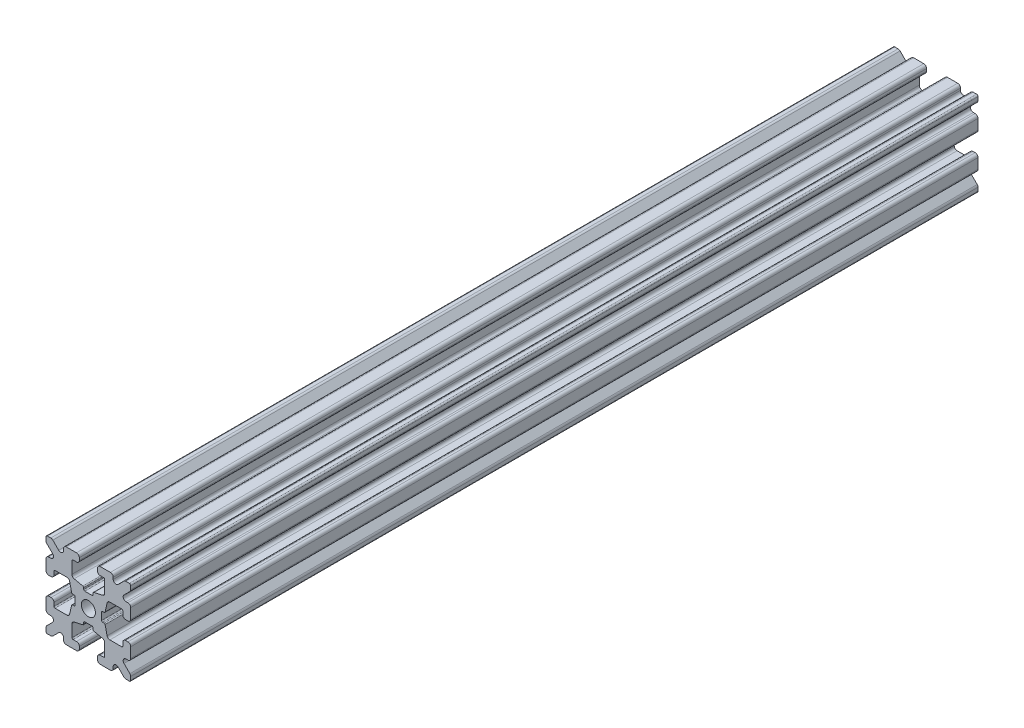
SolidWorks part; units mm, degrees
ref_plane "Front Plane" through (0, 0, 0) normal (0, 0, 1) x (1, 0, 0)
ref_plane "Top Plane" through (0, 0, 0) normal (0, 1, 0) x (1, 0, 0)
ref_plane "Right Plane" through (0, 0, 0) normal (1, 0, 0) x (0, 0, -1)
sketch "Profile" plane through (0, 0, 0) normal (0, 0, 1) x (1, 0, 0)
  line L0 (0.6255, -2.3471) -> (-0.6255, -2.3471)
  line L1 (-0.8255, -2.5471) -> (-0.8255, -2.7749)
  line L2 (-0.9818, -2.97) -> (-2.5094, -3.3124)
  line L3 (-2.9, -3.8003) -> (-2.9, -5.9)
  line L4 (-2.7, -6.1) -> (-2.1, -6.1)
  line L5 (-1.6, -6.6) -> (-1.6, -7)
  line L6 (-4.4, -7) -> (-4.4, -6.6678)
  line L7 (-5.2536, -6.3142) -> (-6.2929, -7.3536)
  line L8 (-7.3536, -6.2929) -> (-6.3142, -5.2536)
  line L9 (-6.6678, -4.4) -> (-7, -4.4)
  line L10 (-7.5, -2.1) -> (-7.5, -3.9)
  line L11 (-7, -1.6) -> (-6.6, -1.6)
  line L12 (-6.1, -2.1) -> (-6.1, -2.7)
  line L13 (-5.9, -2.9) -> (-3.8003, -2.9)
  line L14 (-3.3124, -2.5094) -> (-2.97, -0.9818)
  line L15 (-2.7749, -0.8255) -> (-2.5471, -0.8255)
  line L16 (-2.3471, -0.6255) -> (-2.3471, 0.6255)
  line L17 (-2.5471, 0.8255) -> (-2.7749, 0.8255)
  line L18 (-2.97, 0.9818) -> (-3.3124, 2.5094)
  line L19 (-3.8003, 2.9) -> (-5.9, 2.9)
  line L20 (-6.1, 2.7) -> (-6.1, 2.1)
  line L21 (-6.6, 1.6) -> (-7, 1.6)
  line L22 (-7, 4.4) -> (-6.6678, 4.4)
  line L23 (-6.3142, 5.2536) -> (-7.3536, 6.2929)
  line L24 (-6.2929, 7.3536) -> (-5.2536, 6.3142)
  line L25 (-4.4, 6.6678) -> (-4.4, 7)
  line L26 (-1.6, 7) -> (-1.6, 6.6)
  line L27 (-2.1, 6.1) -> (-2.7, 6.1)
  line L28 (-2.9, 5.9) -> (-2.9, 3.8003)
  line L29 (-2.5094, 3.3124) -> (-0.9818, 2.97)
  line L30 (-0.8255, 2.7749) -> (-0.8255, 2.5471)
  line L31 (-0.6255, 2.3471) -> (0.6255, 2.3471)
  line L32 (0.8255, 2.5471) -> (0.8255, 2.7749)
  line L33 (0.9818, 2.97) -> (2.5094, 3.3124)
  line L34 (2.9, 3.8003) -> (2.9, 5.9)
  line L35 (2.7, 6.1) -> (2.1, 6.1)
  line L36 (1.6, 6.6) -> (1.6, 7)
  line L37 (4.4, 7) -> (4.4, 6.6678)
  line L38 (5.2536, 6.3142) -> (6.2929, 7.3536)
  line L39 (7.25, 7.5) -> (6.6464, 7.5)
  line L40 (7.3536, 6.2929) -> (6.3142, 5.2536)
  line L41 (6.6678, 4.4) -> (7, 4.4)
  line L42 (7, 1.6) -> (6.6, 1.6)
  line L43 (6.1, 2.1) -> (6.1, 2.7)
  line L44 (5.9, 2.9) -> (3.8003, 2.9)
  line L45 (3.3124, 2.5094) -> (2.97, 0.9818)
  line L46 (2.7749, 0.8255) -> (2.5471, 0.8255)
  line L47 (2.3471, 0.6255) -> (2.3471, -0.6255)
  line L48 (2.5471, -0.8255) -> (2.7749, -0.8255)
  line L49 (2.97, -0.9818) -> (3.3124, -2.5094)
  line L50 (3.8003, -2.9) -> (5.9, -2.9)
  line L51 (6.1, -2.7) -> (6.1, -2.1)
  line L52 (6.6, -1.6) -> (7, -1.6)
  line L53 (7.5, -3.9) -> (7.5, -2.1)
  line L54 (7, -4.4) -> (6.6678, -4.4)
  line L55 (6.3142, -5.2536) -> (7.3536, -6.2929)
  line L56 (6.6464, -7.5) -> (7.25, -7.5)
  line L57 (6.2929, -7.3536) -> (5.2536, -6.3142)
  line L58 (4.4, -6.6678) -> (4.4, -7)
  line L59 (1.6, -7) -> (1.6, -6.6)
  line L60 (2.1, -6.1) -> (2.7, -6.1)
  line L61 (2.9, -5.9) -> (2.9, -3.8003)
  line L62 (2.5094, -3.3124) -> (0.9818, -2.97)
  line L63 (0.8255, -2.7749) -> (0.8255, -2.5471)
  line L64 (-7.5, 3.9) -> (-7.5, 2.1)
  line L65 (-6.6464, 7.5) -> (-7.25, 7.5)
  line L66 (-3.9, -7.5) -> (-2.1, -7.5)
  line L67 (7.5, 2.1) -> (7.5, 3.9)
  line L68 (-7.5, 7.25) -> (-7.5, 6.6464)
  line L69 (7.5, -7.25) -> (7.5, -6.6464)
  line L70 (7.5, 6.6464) -> (7.5, 7.25)
  line L71 (-2.1, 7.5) -> (-3.9, 7.5)
  line L72 (-7.5, -6.6464) -> (-7.5, -7.25)
  line L73 (3.9, 7.5) -> (2.1, 7.5)
  line L74 (2.1, -7.5) -> (3.9, -7.5)
  line L75 (-7.25, -7.5) -> (-6.6464, -7.5)
  circle A0 centre (0, 0) radius 1.25
  arc A1 (0.8255, -2.5471) -> (0.6255, -2.3471) centre (0.6255, -2.5471) ccw
  arc A2 (-0.6255, -2.3471) -> (-0.8255, -2.5471) centre (-0.6255, -2.5471) ccw
  arc A3 (-0.9818, -2.97) -> (-0.8255, -2.7749) centre (-1.0255, -2.7749) ccw
  arc A4 (-2.5094, -3.3124) -> (-2.9, -3.8003) centre (-2.4, -3.8003) ccw
  arc A5 (-2.9, -5.9) -> (-2.7, -6.1) centre (-2.7, -5.9) ccw
  arc A6 (-1.6, -6.6) -> (-2.1, -6.1) centre (-2.1, -6.6) ccw
  arc A7 (-2.1, -7.5) -> (-1.6, -7) centre (-2.1, -7) ccw
  arc A8 (-4.4, -7) -> (-3.9, -7.5) centre (-3.9, -7) ccw
  arc A9 (-4.4, -6.6678) -> (-5.2536, -6.3142) centre (-4.9, -6.6678) ccw
  arc A10 (-6.6464, -7.5) -> (-6.2929, -7.3536) centre (-6.6464, -7) ccw
  arc A11 (-7.5, -7.25) -> (-7.25, -7.5) centre (-7.25, -7.25) ccw
  arc A12 (-7.3536, -6.2929) -> (-7.5, -6.6464) centre (-7, -6.6464) ccw
  arc A13 (-6.3142, -5.2536) -> (-6.6678, -4.4) centre (-6.6678, -4.9) ccw
  arc A14 (-7.5, -3.9) -> (-7, -4.4) centre (-7, -3.9) ccw
  arc A15 (-7, -1.6) -> (-7.5, -2.1) centre (-7, -2.1) ccw
  arc A16 (-6.1, -2.1) -> (-6.6, -1.6) centre (-6.6, -2.1) ccw
  arc A17 (-6.1, -2.7) -> (-5.9, -2.9) centre (-5.9, -2.7) ccw
  arc A18 (-3.8003, -2.9) -> (-3.3124, -2.5094) centre (-3.8003, -2.4) ccw
  arc A19 (-2.7749, -0.8255) -> (-2.97, -0.9818) centre (-2.7749, -1.0255) ccw
  arc A20 (-2.5471, -0.8255) -> (-2.3471, -0.6255) centre (-2.5471, -0.6255) ccw
  arc A21 (-2.3471, 0.6255) -> (-2.5471, 0.8255) centre (-2.5471, 0.6255) ccw
  arc A22 (-2.97, 0.9818) -> (-2.7749, 0.8255) centre (-2.7749, 1.0255) ccw
  arc A23 (-3.3124, 2.5094) -> (-3.8003, 2.9) centre (-3.8003, 2.4) ccw
  arc A24 (-5.9, 2.9) -> (-6.1, 2.7) centre (-5.9, 2.7) ccw
  arc A25 (-6.6, 1.6) -> (-6.1, 2.1) centre (-6.6, 2.1) ccw
  arc A26 (-7.5, 2.1) -> (-7, 1.6) centre (-7, 2.1) ccw
  arc A27 (-7, 4.4) -> (-7.5, 3.9) centre (-7, 3.9) ccw
  arc A28 (-6.6678, 4.4) -> (-6.3142, 5.2536) centre (-6.6678, 4.9) ccw
  arc A29 (-7.5, 6.6464) -> (-7.3536, 6.2929) centre (-7, 6.6464) ccw
  arc A30 (-7.25, 7.5) -> (-7.5, 7.25) centre (-7.25, 7.25) ccw
  arc A31 (-6.2929, 7.3536) -> (-6.6464, 7.5) centre (-6.6464, 7) ccw
  arc A32 (-5.2536, 6.3142) -> (-4.4, 6.6678) centre (-4.9, 6.6678) ccw
  arc A33 (-3.9, 7.5) -> (-4.4, 7) centre (-3.9, 7) ccw
  arc A34 (-1.6, 7) -> (-2.1, 7.5) centre (-2.1, 7) ccw
  arc A35 (-2.1, 6.1) -> (-1.6, 6.6) centre (-2.1, 6.6) ccw
  arc A36 (-2.7, 6.1) -> (-2.9, 5.9) centre (-2.7, 5.9) ccw
  arc A37 (-2.9, 3.8003) -> (-2.5094, 3.3124) centre (-2.4, 3.8003) ccw
  arc A38 (-0.8255, 2.7749) -> (-0.9818, 2.97) centre (-1.0255, 2.7749) ccw
  arc A39 (-0.8255, 2.5471) -> (-0.6255, 2.3471) centre (-0.6255, 2.5471) ccw
  arc A40 (0.6255, 2.3471) -> (0.8255, 2.5471) centre (0.6255, 2.5471) ccw
  arc A41 (0.9818, 2.97) -> (0.8255, 2.7749) centre (1.0255, 2.7749) ccw
  arc A42 (2.5094, 3.3124) -> (2.9, 3.8003) centre (2.4, 3.8003) ccw
  arc A43 (2.9, 5.9) -> (2.7, 6.1) centre (2.7, 5.9) ccw
  arc A44 (1.6, 6.6) -> (2.1, 6.1) centre (2.1, 6.6) ccw
  arc A45 (2.1, 7.5) -> (1.6, 7) centre (2.1, 7) ccw
  arc A46 (4.4, 7) -> (3.9, 7.5) centre (3.9, 7) ccw
  arc A47 (4.4, 6.6678) -> (5.2536, 6.3142) centre (4.9, 6.6678) ccw
  arc A48 (6.6464, 7.5) -> (6.2929, 7.3536) centre (6.6464, 7) ccw
  arc A49 (7.5, 7.25) -> (7.25, 7.5) centre (7.25, 7.25) ccw
  arc A50 (7.3536, 6.2929) -> (7.5, 6.6464) centre (7, 6.6464) ccw
  arc A51 (6.3142, 5.2536) -> (6.6678, 4.4) centre (6.6678, 4.9) ccw
  arc A52 (7.5, 3.9) -> (7, 4.4) centre (7, 3.9) ccw
  arc A53 (7, 1.6) -> (7.5, 2.1) centre (7, 2.1) ccw
  arc A54 (6.1, 2.1) -> (6.6, 1.6) centre (6.6, 2.1) ccw
  arc A55 (6.1, 2.7) -> (5.9, 2.9) centre (5.9, 2.7) ccw
  arc A56 (3.8003, 2.9) -> (3.3124, 2.5094) centre (3.8003, 2.4) ccw
  arc A57 (2.7749, 0.8255) -> (2.97, 0.9818) centre (2.7749, 1.0255) ccw
  arc A58 (2.5471, 0.8255) -> (2.3471, 0.6255) centre (2.5471, 0.6255) ccw
  arc A59 (2.3471, -0.6255) -> (2.5471, -0.8255) centre (2.5471, -0.6255) ccw
  arc A60 (2.97, -0.9818) -> (2.7749, -0.8255) centre (2.7749, -1.0255) ccw
  arc A61 (3.3124, -2.5094) -> (3.8003, -2.9) centre (3.8003, -2.4) ccw
  arc A62 (5.9, -2.9) -> (6.1, -2.7) centre (5.9, -2.7) ccw
  arc A63 (6.6, -1.6) -> (6.1, -2.1) centre (6.6, -2.1) ccw
  arc A64 (7.5, -2.1) -> (7, -1.6) centre (7, -2.1) ccw
  arc A65 (7, -4.4) -> (7.5, -3.9) centre (7, -3.9) ccw
  arc A66 (6.6678, -4.4) -> (6.3142, -5.2536) centre (6.6678, -4.9) ccw
  arc A67 (7.5, -6.6464) -> (7.3536, -6.2929) centre (7, -6.6464) ccw
  arc A68 (7.25, -7.5) -> (7.5, -7.25) centre (7.25, -7.25) ccw
  arc A69 (6.2929, -7.3536) -> (6.6464, -7.5) centre (6.6464, -7) ccw
  arc A70 (5.2536, -6.3142) -> (4.4, -6.6678) centre (4.9, -6.6678) ccw
  arc A71 (3.9, -7.5) -> (4.4, -7) centre (3.9, -7) ccw
  arc A72 (1.6, -7) -> (2.1, -7.5) centre (2.1, -7) ccw
  arc A73 (2.1, -6.1) -> (1.6, -6.6) centre (2.1, -6.6) ccw
  arc A74 (2.7, -6.1) -> (2.9, -5.9) centre (2.7, -5.9) ccw
  arc A75 (2.9, -3.8003) -> (2.5094, -3.3124) centre (2.4, -3.8003) ccw
  arc A76 (0.8255, -2.7749) -> (0.9818, -2.97) centre (1.0255, -2.7749) ccw
extrude "Boss-Extrude1" add sketch "Profile" against normal blind 150
